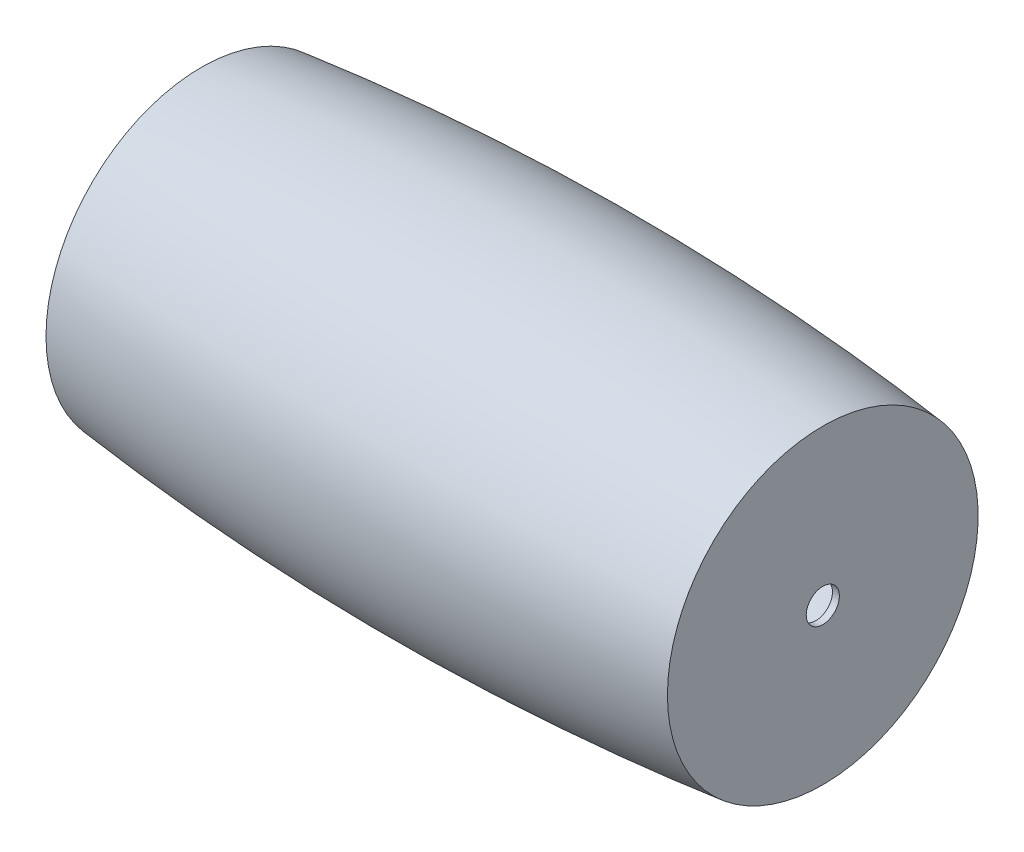
SolidWorks part; units mm, degrees
ref_plane "Спереди" through (0, 0, 0) normal (0, 0, 1) x (1, 0, 0)
ref_plane "Сверху" through (0, 0, 0) normal (0, 1, 0) x (1, 0, 0)
ref_plane "Справа" through (0, 0, 0) normal (1, 0, 0) x (0, 0, -1)
sketch "Эскиз1" plane through (0, 0, 0) normal (0, 0, 1) x (1, 0, 0)
  line L0 (0, 21.9204) -> (0, 31.9825)
  line L1 (900, -193.0175) -> (900, 31.9825)
  line L2 (890, -193.0175) -> (900, -193.0175)
  line L3 (890, -183.0175) -> (890, 23.0252) construction
  line L4 (890, -193.0175) -> (890, 23.0252)
  line L5 (0, -193.0175) -> (0, 31.9825) construction
  line L6 (10, -183.0175) -> (10, 23.0252) construction
  line L7 (10, -183.0175) -> (890, -183.0175) construction
  line L8 (0, -193.0175) -> (900, -193.0175) construction
  arc A0 (0, 31.9825) -> (900, 31.9825) centre (450, -4005.5175) cw
  arc A1 (0, 21.9204) -> (890, 23.0252) centre (450, -4005.5175) cw
  arc A2 (10, 23.0252) -> (890, 23.0252) centre (450, -4005.5175) cw construction
  dimension "D2" = 900
  dimension "D4" = 10
revolve "Повернуть1" add sketch "Эскиз1" angle 360 about L2
sketch "Эскиз2" plane through (0, 0, 0) normal (-1, 0, 0) x (0, 0, 1)
  circle A0 centre (0, -193.0175) radius 24
  dimension "D1" = 48
extrude "Вырез-Вытянуть1" cut sketch "Эскиз2" against normal through all
